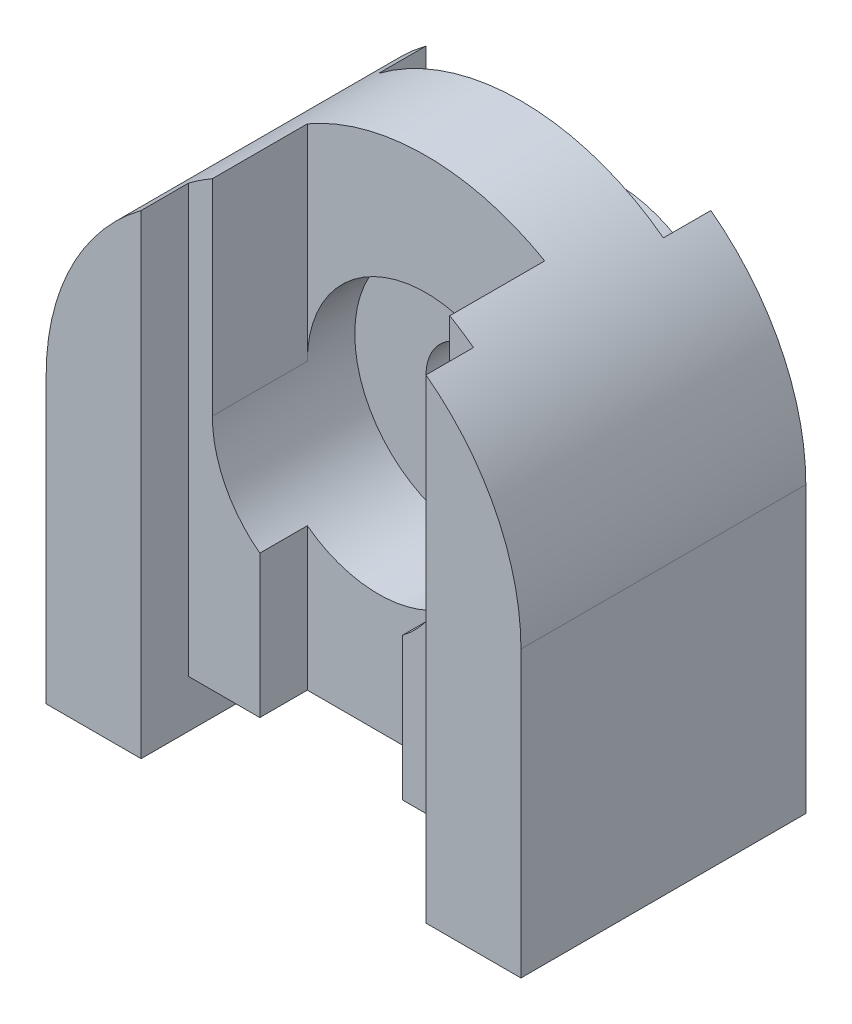
SolidWorks part; units mm, degrees
ref_plane "Front Plane" through (0, 0, 0) normal (0, 0, 1) x (1, 0, 0)
ref_plane "Top Plane" through (0, 0, 0) normal (0, 1, 0) x (1, 0, 0)
ref_plane "Right Plane" through (0, 0, 0) normal (1, 0, 0) x (0, 0, -1)
sketch "Sketch1" plane through (0, 0, 0) normal (0, 0, 1) x (1, 0, 0)
  line L1 (0, 0) -> (100, 0)
  line L2 (0, 0) -> (0, 110)
  line L3 (0, 110) -> (100, 110)
  line L4 (100, 0) -> (100, 110)
  dimension "D1" = 100
  dimension "D2" = 110
extrude "Boss-Extrude1" add sketch "Sketch1" along normal blind 70
sketch "Sketch2" plane through (0, 0, 70) normal (0, 0, 1) x (1, 0, 0)
  line L0 (0, 0) -> (100, 0) construction
  line L1 (20, 0) -> (80, 0)
  line L2 (20, 0) -> (20, 10)
  line L3 (20, 10) -> (80, 10)
  line L4 (80, 0) -> (80, 10)
  dimension "D1" = 60
  dimension "D2" = 20
  dimension "D3" = 10
extrude "Cut-Extrude1" cut sketch "Sketch2" against normal blind 70
sketch "Sketch3" plane through (0, 0, 70) normal (0, 0, 1) x (1, 0, 0)
  line L0 (0, 110) -> (0, 0) construction
  line L1 (100, 0) -> (100, 110) construction
  line L2 (100, 110) -> (0, 110) construction
  line L3 (0, 60) -> (0, 110)
  line L4 (0, 110) -> (100, 110)
  line L5 (100, 110) -> (100, 60)
  arc A0 (0, 60) -> (100, 60) centre (50, 60) cw
  line M6 (100, 0) -> (100, 110)
  line M7 (100, 110) -> (0, 110)
  line M8 (0, 110) -> (0, 0)
  dimension "D1" = 60
  dimension "D2" = 0
  dimension "D3" = 0
  dimension "D4" = 50
  dimension "D5" = 50
extrude "Cut-Extrude2" cut sketch "Sketch3" against normal blind 70 contours A0 L4 M8 | A0 M7 M6
sketch "Sketch4" plane through (0, 0, 0) normal (0, 0, -1) x (-1, 0, 0)
  circle A0 centre (-50, 60) radius 10
  dimension "D1" = 20
extrude "Cut-Extrude3" cut sketch "Sketch4" against normal blind 30
sketch "Sketch5" plane through (0, 0, 0) normal (0, -1, 0) x (1, 0, 0)
  line L0 (100, 70) -> (100, 0) construction
  line L1 (0, 0) -> (100, 0)
  line L2 (0, 0) -> (0, 10)
  line L3 (0, 10) -> (100, 10)
  line L4 (100, 0) -> (100, 10)
  dimension "D1" = 10
extrude "Cut-Extrude4" cut sketch "Sketch5" against normal blind 185
sketch "Sketch7" plane through (0, 10, 0) normal (0, -1, 0) x (-1, 0, 0)
  line L0 (-20, -10) -> (-80, -10) construction
  line L1 (-20, -10) -> (-80, -10)
  line L2 (-20, -10) -> (-20, -20)
  line L3 (-20, -20) -> (-80, -20)
  line L4 (-80, -10) -> (-80, -20)
  dimension "D1" = 20
  dimension "D2" = 20
  dimension "D3" = 10
extrude "Cut-Extrude5" cut sketch "Sketch7" against normal blind 200
sketch "Sketch8" plane through (0, 0, 20) normal (0, 0, -1) x (-1, 0, 0)
  circle A0 centre (-50, 60) radius 25
  circle A1 centre (-50, 60) radius 10
  dimension "D1" = 50
  dimension "D2" = 20
extrude "Boss-Extrude3" add sketch "Sketch8" along normal blind 20
sketch "Sketch9" plane through (0, 0, 70) normal (0, 0, 1) x (1, 0, 0)
  circle A0 centre (50, 60) radius 25
  dimension "D1" = 50
extrude "Cut-Extrude7" cut sketch "Sketch9" against normal blind 40
sketch "Sketch10" plane through (0, 0, 70) normal (0, 0, 1) x (1, 0, 0)
  line L0 (25, 60) -> (25, 103.3013)
  line L1 (75, 60) -> (75, 103.3013)
  line L2 (25, 103.3013) -> (25, 60)
  circle A0 centre (50, 60) radius 25 construction
  arc A1 (100, 60) -> (0, 60) centre (50, 60) ccw construction
  arc A2 (25, 103.3013) -> (75, 103.3013) centre (50, 60) cw
  circle M4 centre (50, 60) radius 25
  arc M6 (100, 60) -> (0, 60) centre (50, 60) ccw
extrude "Cut-Extrude8" cut sketch "Sketch10" against normal blind 30 contours L1 L0 M4 M6
sketch "Sketch11" plane through (0, 10, 0) normal (0, -1, 0) x (-1, 0, 0)
  line L0 (-80, -70) -> (-20, -70) construction
  line L1 (-20, -70) -> (-80, -70)
  line L2 (-20, -70) -> (-20, -60)
  line L3 (-20, -60) -> (-80, -60)
  line L4 (-80, -70) -> (-80, -60)
  dimension "D1" = 20
  dimension "D2" = 20
  dimension "D3" = 10
extrude "Cut-Extrude9" cut sketch "Sketch11" against normal blind 130
sketch "Sketch12" plane through (0, 10, 0) normal (0, -1, 0) x (1, 0, 0)
  line L0 (20, 60) -> (80, 60) construction
  line L1 (35, 60) -> (65, 60)
  line L2 (35, 60) -> (35, 50)
  line L3 (35, 50) -> (65, 50)
  line L4 (65, 60) -> (65, 50)
  dimension "D1" = 30
  dimension "D2" = 10
  dimension "D3" = 35
extrude "Cut-Extrude10" cut sketch "Sketch12" against normal blind 130
